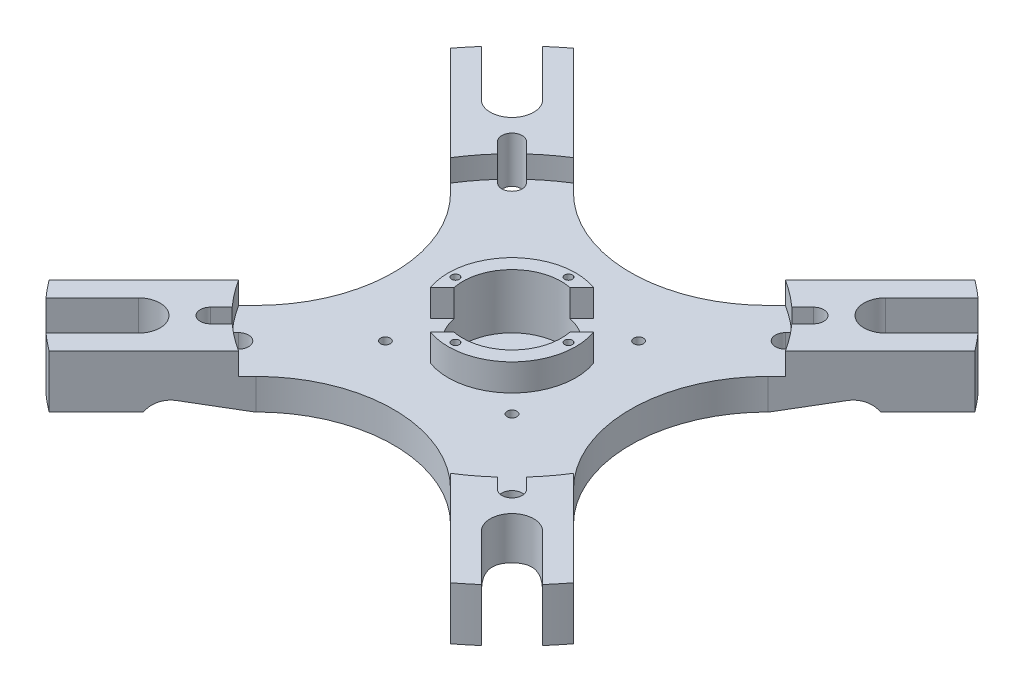
SolidWorks part; units mm, degrees
ref_plane "Front Plane" through (0, 0, 0) normal (0, 0, 1) x (1, 0, 0)
ref_plane "Top Plane" through (0, 0, 0) normal (0, 1, 0) x (1, 0, 0)
ref_plane "Right Plane" through (0, 0, 0) normal (1, 0, 0) x (0, 0, -1)
sketch "Sketch1" plane through (0, 0, 0) normal (0, 1, 0) x (1, 0, 0)
  line L0 (0, 320.3285) -> (0, -348.3018) construction
  line L1 (-201.6125, -201.6125) -> (201.6125, -201.6125)
  line L2 (-201.6125, -201.6125) -> (-201.6125, 201.6125)
  line L3 (-201.6125, 201.6125) -> (201.6125, 201.6125)
  line L4 (201.6125, -201.6125) -> (201.6125, 201.6125)
  line L5 (-219.6928, 0) -> (370.4758, 0) construction
  dimension "D1" = 403.225
extrude "Boss-Extrude1" add sketch "Sketch1" along normal blind 12.192
fillet "Fillet1" radius 38.1 4 edges at (-201.6125, 6.096, -201.6125) (201.6125, 6.096, -201.6125) (201.6125, 6.096, 201.6125) (-201.6125, 6.096, 201.6125)
sketch "Sketch2" plane through (0, 12.192, 0) normal (0, 1, 0) x (1, 0, 0)
  line L0 (0, 0) -> (-190.4533, -190.4533) construction
  line L1 (0, 0) -> (190.4533, 190.4533) construction
  line L2 (0, 0) -> (190.4533, -190.4533) construction
  line L3 (0, 0) -> (-190.4533, 190.4533) construction
  line L4 (-22.4506, 36.6394) -> (-132.2432, 146.432)
  line L5 (-36.6394, -22.4506) -> (-146.432, -132.2432)
  line L6 (36.6394, 22.4506) -> (146.432, 132.2432)
  line L7 (22.4506, -36.6394) -> (132.2432, -146.432)
  line L8 (-36.6394, 22.4506) -> (-146.432, 132.2432)
  line L9 (-22.4506, -36.6394) -> (-132.2432, -146.432)
  line L10 (22.4506, 36.6394) -> (132.2432, 146.432)
  line L11 (36.6394, -22.4506) -> (146.432, -132.2432)
  line L32 (7.0944, 7.0944) -> (197.5477, -183.3589) construction
  line L33 (7.0944, -7.0944) -> (197.5477, 183.3589) construction
  line L34 (-7.0944, 7.0944) -> (183.3589, 197.5477) construction
  line L35 (7.0944, 7.0944) -> (-183.3589, 197.5477) construction
  line L36 (191.9605, -163.5125) -> (191.9605, 163.5125)
  line L37 (163.5125, 191.9605) -> (-163.5125, 191.9605)
  line L38 (-163.5125, -191.9605) -> (163.5125, -191.9605)
  line L39 (-191.9605, 163.5125) -> (-191.9605, -163.5125)
  line L40 (191.9605, -113.3846) -> (191.9605, 113.3846)
  line L41 (113.3846, 191.9605) -> (-113.3846, 191.9605)
  line L42 (-113.3846, -191.9605) -> (113.3846, -191.9605)
  line L43 (-191.9605, 113.3846) -> (-191.9605, -113.3846)
  line L44 (-7.0944, 7.0944) -> (-197.5477, -183.3589) construction
  line L45 (-7.0944, -7.0944) -> (-197.5477, 183.3589) construction
  line L46 (-7.0944, -7.0944) -> (183.3589, -197.5477) construction
  line L47 (7.0944, -7.0944) -> (-183.3589, -197.5477) construction
  arc A0 (-201.6125, -163.5125) -> (-163.5125, -201.6125) centre (-163.5125, -163.5125) ccw construction
  arc A1 (201.6125, 163.5125) -> (163.5125, 201.6125) centre (163.5125, 163.5125) ccw construction
  arc A2 (163.5125, -201.6125) -> (201.6125, -163.5125) centre (163.5125, -163.5125) ccw construction
  arc A3 (-163.5125, 201.6125) -> (-201.6125, 163.5125) centre (-163.5125, 163.5125) ccw construction
  arc A20 (36.6394, -22.4506) -> (36.6394, 22.4506) centre (59.0901, 0) cw
  arc A21 (22.4506, 36.6394) -> (-22.4506, 36.6394) centre (0, 59.0901) cw
  arc A22 (-36.6394, -22.4506) -> (-36.6394, 22.4506) centre (-59.0901, 0) ccw
  arc A23 (22.4506, -36.6394) -> (-22.4506, -36.6394) centre (0, -59.0901) ccw
  arc A24 (163.5125, -191.9605) -> (191.9605, -163.5125) centre (163.5125, -163.5125) ccw
  arc A25 (191.9605, 163.5125) -> (163.5125, 191.9605) centre (163.5125, 163.5125) ccw
  arc A26 (-163.5125, 191.9605) -> (-191.9605, 163.5125) centre (-163.5125, 163.5125) ccw
  arc A27 (-191.9605, -163.5125) -> (-163.5125, -191.9605) centre (-163.5125, -163.5125) ccw
  arc A28 (163.5125, -191.9605) -> (191.9605, -163.5125) centre (163.5125, -163.5125) ccw
  arc A29 (191.9605, 163.5125) -> (163.5125, 191.9605) centre (163.5125, 163.5125) ccw
  arc A30 (-163.5125, 191.9605) -> (-191.9605, 163.5125) centre (-163.5125, 163.5125) ccw
  arc A31 (-191.9605, -163.5125) -> (-163.5125, -191.9605) centre (-163.5125, -163.5125) ccw
  arc A32 (-113.3846, -191.9605) -> (-132.2432, -146.432) centre (-113.3846, -165.2905) cw
  arc A33 (113.3846, -191.9605) -> (132.2432, -146.432) centre (113.3846, -165.2905) ccw
  arc A34 (146.432, -132.2432) -> (191.9605, -113.3846) centre (165.2905, -113.3846) ccw
  arc A35 (146.432, 132.2432) -> (191.9605, 113.3846) centre (165.2905, 113.3846) cw
  arc A36 (113.3846, 191.9605) -> (132.2432, 146.432) centre (113.3846, 165.2905) cw
  arc A37 (-113.3846, 191.9605) -> (-132.2432, 146.432) centre (-113.3846, 165.2905) ccw
  arc A38 (-191.9605, 113.3846) -> (-146.432, 132.2432) centre (-165.2905, 113.3846) cw
  arc A39 (-191.9605, -113.3846) -> (-146.432, -132.2432) centre (-165.2905, -113.3846) ccw
  dimension "D4" = 31.75
  dimension "D5" = 26.67
  dimension "D1" = 10.033
  dimension "D2" = 10.033
  dimension "D3" = 9.652
extrude "Cut-Extrude1" cut sketch "Sketch2" against normal blind 12.192 contours L43 A39 L5 A22 L8 A38 | L42 A33 L7 A23 L9 A32 | A35 L6 A20 L11 A34 L40 | L41 A37 L4 A21 L10 A36
sketch "Sketch3" plane through (0, 12.192, 0) normal (0, 1, 0) x (1, 0, 0)
  circle A0 centre (0, 0) radius 45.72
  dimension "D1" = 91.44
extrude "Cut-Extrude2" cut sketch "Sketch3" against normal blind 5.08
sketch "Sketch5" plane through (0, 7.112, 0) normal (0, 1, 0) x (1, 0, 0)
  circle A0 centre (0, 0) radius 11.3665
  dimension "D1" = 22.733
extrude "Cut-Extrude4" cut sketch "Sketch5" against normal blind 6.4262
sketch "Sketch6" plane through (0, 0.6858, 0) normal (0, 1, 0) x (1, 0, 0)
  circle A0 centre (0, 0) radius 4.7117
  dimension "D1" = 9.4234
extrude "Cut-Extrude5" cut sketch "Sketch6" against normal through all
sketch "Sketch7" plane through (0, 7.112, 0) normal (0, 1, 0) x (1, 0, 0)
  line L0 (0, 0) -> (32.3289, 32.3289) construction
  line L1 (0, 0) -> (-32.3289, -32.3289) construction
  line L2 (2.176, 11.1563) -> (4.9096, 13.8898)
  line L3 (-11.1563, -2.176) -> (-13.8898, -4.9096)
  line L4 (11.1563, 2.176) -> (13.8898, 4.9096)
  line L5 (-2.176, -11.1563) -> (-4.9096, -13.8898)
  line L6 (-4.4901, 4.4901) -> (-36.8191, -27.8388) construction
  line L7 (4.4901, -4.4901) -> (-27.8388, -36.8191) construction
  line L8 (-4.4901, 4.4901) -> (27.8388, 36.8191) construction
  line L9 (4.4901, -4.4901) -> (36.8191, 27.8388) construction
  arc A0 (-4.9096, -13.8898) -> (13.8898, 4.9096) centre (0, 0) ccw
  arc A1 (38.6353, 24.4465) -> (24.4465, 38.6353) centre (0, 0) ccw construction
  arc A2 (-38.6353, -24.4465) -> (-24.4465, -38.6353) centre (0, 0) ccw construction
  arc A3 (4.9096, 13.8898) -> (-13.8898, -4.9096) centre (0, 0) ccw
  circle A4 centre (0, 0) radius 11.3665 construction
  arc A5 (-2.176, -11.1563) -> (11.1563, 2.176) centre (0, 0) ccw
  arc A6 (2.176, 11.1563) -> (-11.1563, -2.176) centre (0, 0) ccw
  dimension "D1" = 29.464
  dimension "D2" = 6.35
  dimension "D3" = 6.35
extrude "Boss-Extrude2" add sketch "Sketch7" along normal blind 6.223
hole_wizard "#2-56 Tapped Hole1" positions "Sketch9" profile "Sketch8" tap size "#2-56" standard "ANSI Inch"
sketch "Sketch9" plane through (0, 13.335, 0) normal (0, 1, 0) x (1, 0, 0)
  line L0 (0, 11.3665) -> (0, 13.0492) construction
  line L1 (0, 13.0492) -> (0, 14.732) construction
  line L2 (0, 0) -> (-13.0492, 0) construction
  line L3 (0, 0) -> (0, -13.0492) construction
  line L4 (0, 0) -> (13.0492, 0) construction
  circle A0 centre (0, 0) radius 13.0492
  circle A1 centre (0, 0) radius 11.3665 construction
  arc A2 (4.9096, 13.8898) -> (-13.8898, -4.9096) centre (0, 0) ccw construction
  point P0 (0, 13.0492)
  point P2 (-13.0492, 0)
  point P4 (0, -13.0492)
  point P6 (13.0492, 0)
sketch "Sketch8" plane through (0, 13.335, -13.0492) normal (1, 0, 0) x (0, 0, 1)
  line L0 (0, 0) -> (0, 6.1222)
  line L1 (0, 6.1222) -> (0.889, 5.588)
  line L2 (0.889, 5.588) -> (0.889, 0)
  line L5 (0.889, 0) -> (0, 0)
  line L10 (0, 6.1222) -> (-0.889, 5.588) construction
  line L11 (0, -6.35) -> (0, 107.95) construction
  dimension "Tap Drill Dia." = 1.778
  dimension "Tap Drill Depth" = 5.588
  dimension "Drill Angle" = 118
cosmetic thread "Hole Thread1" parameters "D1"=4.318, "D2"=2.1844
cosmetic thread "Hole Thread2" parameters "D1"=4.318, "D2"=2.1844
cosmetic thread "Hole Thread3" parameters "D1"=4.318, "D2"=2.1844
cosmetic thread "Hole Thread4" parameters "D1"=4.318, "D2"=2.1844
hole_wizard "#4-40 Tapped Hole1" positions "Sketch11" profile "Sketch10" tap size "#4-40" standard "ANSI Inch" end condition through all
sketch "Sketch11" plane through (0, 7.112, 0) normal (0, 1, 0) x (1, 0, 0)
  line L0 (0, 0) -> (-32.3289, 32.3289) construction
  line L1 (0, 0) -> (32.3289, 32.3289) construction
  line L2 (0, 0) -> (36.361, -36.361) construction
  line L3 (0, 0) -> (-32.3289, -32.3289) construction
  arc A0 (-24.4465, 38.6353) -> (-38.6353, 24.4465) centre (0, 0) ccw construction
  arc A1 (38.6353, 24.4465) -> (24.4465, 38.6353) centre (0, 0) ccw construction
  arc A2 (-38.6353, -24.4465) -> (-24.4465, -38.6353) centre (0, 0) ccw construction
  point P0 (-14.605, 14.605)
  point P2 (14.605, 14.605)
  point P4 (-14.605, -14.605)
  point P6 (14.605, -14.605)
  dimension "D1" = 29.21
sketch "Sketch10" plane through (-14.605, 7.112, -14.605) normal (1, 0, 0) x (0, 0, 1)
  line L0 (0, 0) -> (0, 7.112)
  line L1 (0, 7.112) -> (1.1303, 7.112)
  line L2 (1.1303, 7.112) -> (1.1303, 0)
  line L5 (1.1303, 0) -> (0, 0)
  line L11 (0, -6.35) -> (0, 107.95) construction
  dimension "Thru Tap Drill Dia." = 2.2606
  dimension "Thru Tap Drill Depth" = 7.112
cosmetic thread "Hole Thread5" parameters "D2"=2.8448
cosmetic thread "Hole Thread6" parameters "D2"=2.8448
cosmetic thread "Hole Thread7" parameters "D2"=2.8448
cosmetic thread "Hole Thread8" parameters "D2"=2.8448
sketch "Sketch12" plane through (0, 12.192, 0) normal (0, 1, 0) x (1, 0, 0)
  line L0 (34.7985, 34.7985) -> (31.5656, 31.5656) construction
  line L1 (36.4598, 33.1371) -> (33.2269, 29.9043)
  line L2 (33.1371, 36.4598) -> (29.9043, 33.2269)
  line L3 (0, 0) -> (32.3289, 32.3289) construction
  line L4 (34.7985, -34.7985) -> (31.5656, -31.5656) construction
  line L5 (33.1371, -36.4598) -> (29.9043, -33.2269)
  line L6 (36.4598, -33.1371) -> (33.2269, -29.9043)
  line L7 (-34.7985, -34.7985) -> (-31.5656, -31.5656) construction
  line L8 (-36.4598, -33.1371) -> (-33.2269, -29.9043)
  line L9 (-33.1371, -36.4598) -> (-29.9043, -33.2269)
  line L10 (-34.7985, 34.7985) -> (-31.5656, 31.5656) construction
  line L11 (-33.1371, 36.4598) -> (-29.9043, 33.2269)
  line L12 (-36.4598, 33.1371) -> (-33.2269, 29.9043)
  arc A0 (36.4598, 33.1371) -> (33.1371, 36.4598) centre (34.7985, 34.7985) ccw
  arc A1 (29.9043, 33.2269) -> (33.2269, 29.9043) centre (31.5656, 31.5656) ccw
  arc A2 (38.6353, 24.4465) -> (24.4465, 38.6353) centre (0, 0) ccw construction
  arc A3 (33.1371, -36.4598) -> (36.4598, -33.1371) centre (34.7985, -34.7985) ccw
  arc A4 (33.2269, -29.9043) -> (29.9043, -33.2269) centre (31.5656, -31.5656) ccw
  arc A5 (-36.4598, -33.1371) -> (-33.1371, -36.4598) centre (-34.7985, -34.7985) ccw
  arc A6 (-29.9043, -33.2269) -> (-33.2269, -29.9043) centre (-31.5656, -31.5656) ccw
  arc A7 (-33.1371, 36.4598) -> (-36.4598, 33.1371) centre (-34.7985, 34.7985) ccw
  arc A8 (-33.2269, 29.9043) -> (-29.9043, 33.2269) centre (-31.5656, 31.5656) ccw
  point P2 (33.182, 33.182)
  point P18 (33.182, -33.182)
  point P25 (-33.182, -33.182)
  point P32 (-33.182, 33.182)
  point P37 (0, 0)
  dimension "D1" = 4.699
  dimension "D2" = 4.572
  dimension "D3" = 49.2125
  dimension "D4" = 4
extrude "Cut-Extrude6" cut sketch "Sketch12" against normal through all both and the other way through all
sketch "Sketch13" plane through (0, 0, 0) normal (0, 0, 1) x (1, 0, 0)
  line L0 (0, 0) -> (0, 13.335) construction
  line L1 (14.732, 13.335) -> (-4.9096, 13.335) construction
  line L2 (43.18, 0) -> (55.626, 2.286)
  line L3 (-163.5125, 0) -> (163.5125, 0) construction
  line L4 (43.18, 0) -> (60.96, 0)
  arc A0 (55.626, 2.286) -> (60.96, 0) centre (56.5731, -2.8702) cw
  dimension "D1" = 43.18
  dimension "D2" = 2.286
  dimension "D3" = 55.626
  dimension "D4" = 60.96
revolve "Cut-Revolve1" cut sketch "Sketch13" angle 360 about L0
sketch "Sketch14" plane through (0, 0, 0) normal (0, -1, 0) x (1, 0, 0)
  line L0 (0, 0) -> (-190.4533, 190.4533) construction
  line L1 (-144.5821, 144.5821) -> (-43.1052, 43.1052) construction
  line L2 (-141.0529, 148.1114) -> (-39.576, 46.6345)
  line L3 (-148.1114, 141.0529) -> (-46.6345, 39.576)
  line L4 (144.5821, 144.5821) -> (43.1052, 43.1052) construction
  line L5 (148.1114, 141.0529) -> (46.6345, 39.576)
  line L6 (141.0529, 148.1114) -> (39.576, 46.6345)
  line L7 (144.5821, -144.5821) -> (43.1052, -43.1052) construction
  line L8 (141.0529, -148.1114) -> (39.576, -46.6345)
  line L9 (148.1114, -141.0529) -> (46.6345, -39.576)
  line L10 (-144.5821, -144.5821) -> (-43.1052, -43.1052) construction
  line L11 (-148.1114, -141.0529) -> (-46.6345, -39.576)
  line L12 (-141.0529, -148.1114) -> (-39.576, -46.6345)
  arc A0 (-163.5125, 201.6125) -> (-201.6125, 163.5125) centre (-163.5125, 163.5125) ccw construction
  arc A1 (-141.0529, 148.1114) -> (-148.1114, 141.0529) centre (-144.5821, 144.5821) ccw
  arc A2 (-46.6345, 39.576) -> (-39.576, 46.6345) centre (-43.1052, 43.1052) ccw
  arc A3 (148.1114, 141.0529) -> (141.0529, 148.1114) centre (144.5821, 144.5821) ccw
  arc A4 (39.576, 46.6345) -> (46.6345, 39.576) centre (43.1052, 43.1052) ccw
  arc A5 (141.0529, -148.1114) -> (148.1114, -141.0529) centre (144.5821, -144.5821) ccw
  arc A6 (46.6345, -39.576) -> (39.576, -46.6345) centre (43.1052, -43.1052) ccw
  arc A7 (-148.1114, -141.0529) -> (-141.0529, -148.1114) centre (-144.5821, -144.5821) ccw
  arc A8 (-39.576, -46.6345) -> (-46.6345, -39.576) centre (-43.1052, -43.1052) ccw
  point P8 (-93.8437, 93.8437)
  point P18 (93.8437, 93.8437)
  point P25 (93.8437, -93.8437)
  point P32 (-93.8437, -93.8437)
  point P37 (0, 0)
  arc M3 (49.6118, -35.423) -> (35.423, -49.6118) centre (0, 0) cw
  arc M9 (-35.423, -49.6118) -> (-49.6118, -35.423) centre (0, 0) cw
  arc M15 (-49.6118, 35.423) -> (-35.423, 49.6118) centre (0, 0) cw
  arc M21 (35.423, 49.6118) -> (49.6118, 35.423) centre (0, 0) cw
  dimension "D1" = 9.9822
  dimension "D2" = 60.96
  dimension "D3" = 143.51
  dimension "D4" = 4
extrude "Cut-Extrude10" cut sketch "Sketch14" against normal through all contours A2 L2 A1 L3 M15 | A4 L5 A3 L6 M21 | A4 M21 | A2 M15 | L9 A6 L8 A5 M3 | A6 M3 | A8 M9 | L12 A8 L11 A7 M9
sketch "Sketch15" plane through (0, 0, 0) normal (0, -1, 0) x (1, 0, 0)
  circle A0 centre (0, 0) radius 76.2
  circle A1 centre (0, 0) radius 269.3416
  dimension "D1" = 152.4
extrude "Cut-Extrude11" cut sketch "Sketch15" against normal through all
